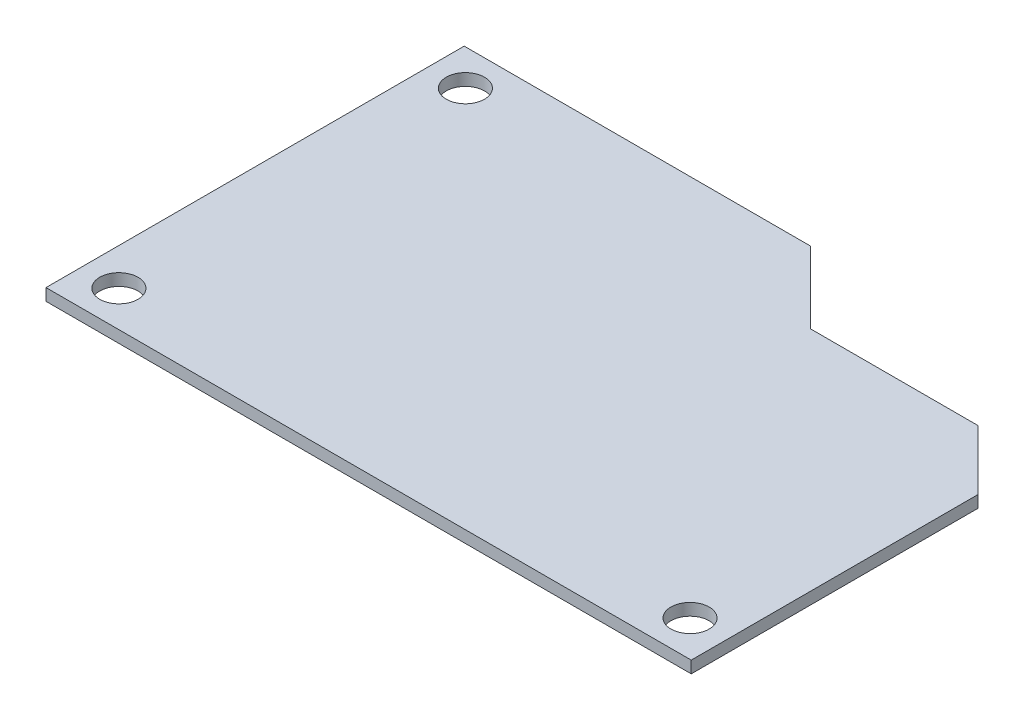
SolidWorks part; units mm, degrees
ref_plane "Спереди" through (0, 0, 0) normal (0, 0, 1) x (1, 0, 0)
ref_plane "Сверху" through (0, 0, 0) normal (0, 1, 0) x (1, 0, 0)
ref_plane "Справа" through (0, 0, 0) normal (1, 0, 0) x (0, 0, -1)
sketch "Эскиз1" plane through (0, 0, 0) normal (0, 1, 0) x (1, 0, 0)
  line L1 (-27, 17.5) -> (27, 17.5)
  line L2 (-27, 17.5) -> (-27, -17.5)
  line L3 (-27, -17.5) -> (27, -17.5)
  line L4 (27, 17.5) -> (27, -17.5)
  line L5 (-27, 17.5) -> (27, -17.5) construction
  line L6 (-27, -17.5) -> (27, 17.5) construction
  point P0 (0, 0)
  dimension "D1" = 54
  dimension "D2" = 35
extrude "Бобышка-Вытянуть1" add sketch "Эскиз1" along normal blind 1
sketch "Эскиз2" plane through (0, 1, 0) normal (0, 1, 0) x (1, 0, 0)
  line L0 (2, 17.5) -> (8, 11.5)
  line L1 (27, 17.5) -> (-27, 17.5) construction
  line L2 (8, 11.5) -> (22, 11.5)
  line L3 (22, 11.5) -> (27, 6.5)
  line L4 (27, -17.5) -> (27, 17.5) construction
  line L5 (27, 6.5) -> (27, 17.5)
  line L6 (27, 17.5) -> (2, 17.5)
  line L7 (-27, 17.5) -> (-27, -17.5) construction
  point P12 (19.3806, 11.3631)
  dimension "D1" = 29
  dimension "D2" = 14
  dimension "D3" = 6
  dimension "D4" = 5
  dimension "D5" = 6
  dimension "D6" = 5
extrude "Вырез-Вытянуть1" cut sketch "Эскиз2" against normal up to surface (1 mm away) up to face at (0, 0, 0)
sketch "Эскиз3" plane through (0, 1, 0) normal (0, 1, 0) x (1, 0, 0)
  line L0 (0, -17.5) -> (0, 17.5) construction
  line L1 (-27, -17.5) -> (27, -17.5) construction
  line L2 (2, 17.5) -> (-27, 17.5) construction
  line L3 (-27, 0) -> (27, 0) construction
  line L4 (-27, 17.5) -> (-27, -17.5) construction
  line L5 (27, -17.5) -> (27, 6.5) construction
  line L6 (-23.9, 17.5) -> (-23.9, 0) construction
  line L7 (-27, 14.5) -> (0, 14.5) construction
  circle A0 centre (-23.9, 14.5) radius 1.6
  circle A1 centre (-23.9, -14.5) radius 1.6
  circle A2 centre (23.9, -14.5) radius 1.6
  dimension "D3" = 3.2
  dimension "D1" = 3
  dimension "D2" = 3.1
extrude "Вырез-Вытянуть2" cut sketch "Эскиз3" against normal up to surface (1 mm away) up to face at (4.5714, 0, -4.2143)
